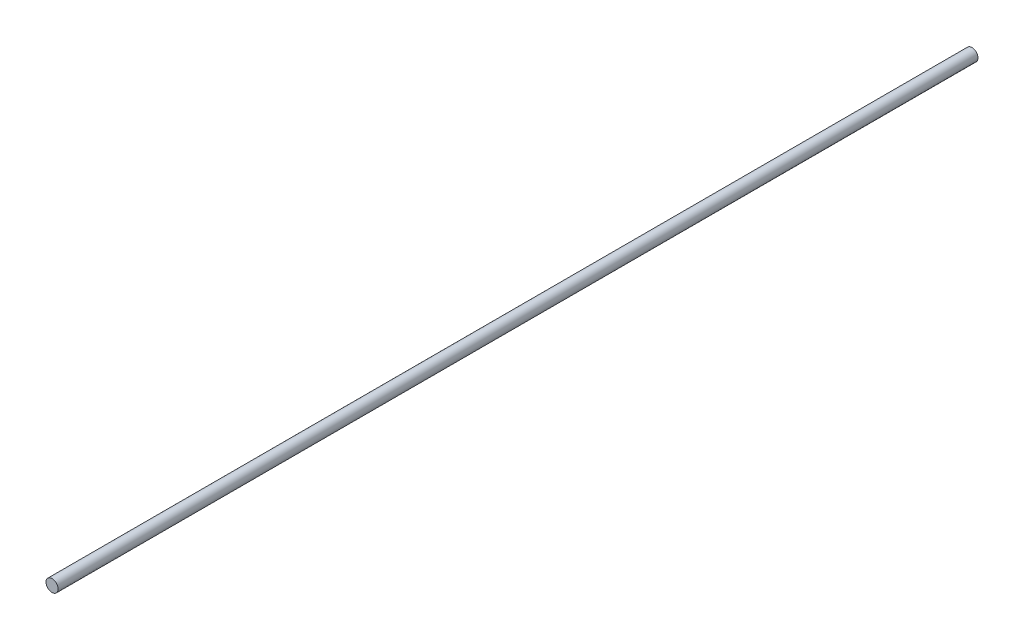
SolidWorks part; units mm, degrees
material "6061 Alloy"
ref_plane "Front Plane" through (0, 0, 0) normal (0, 0, 1) x (1, 0, 0)
ref_plane "Top Plane" through (0, 0, 0) normal (0, 1, 0) x (1, 0, 0)
ref_plane "Right Plane" through (0, 0, 0) normal (1, 0, 0) x (0, 0, -1)
sketch "Sketch1" plane through (0, 0, 0) normal (0, 0, 1) x (1, 0, 0)
  circle A0 centre (0, 0) radius 3.175
  dimension "D1" = 6.35
extrude "Boss-Extrude1" add sketch "Sketch1" along normal blind 482.6
